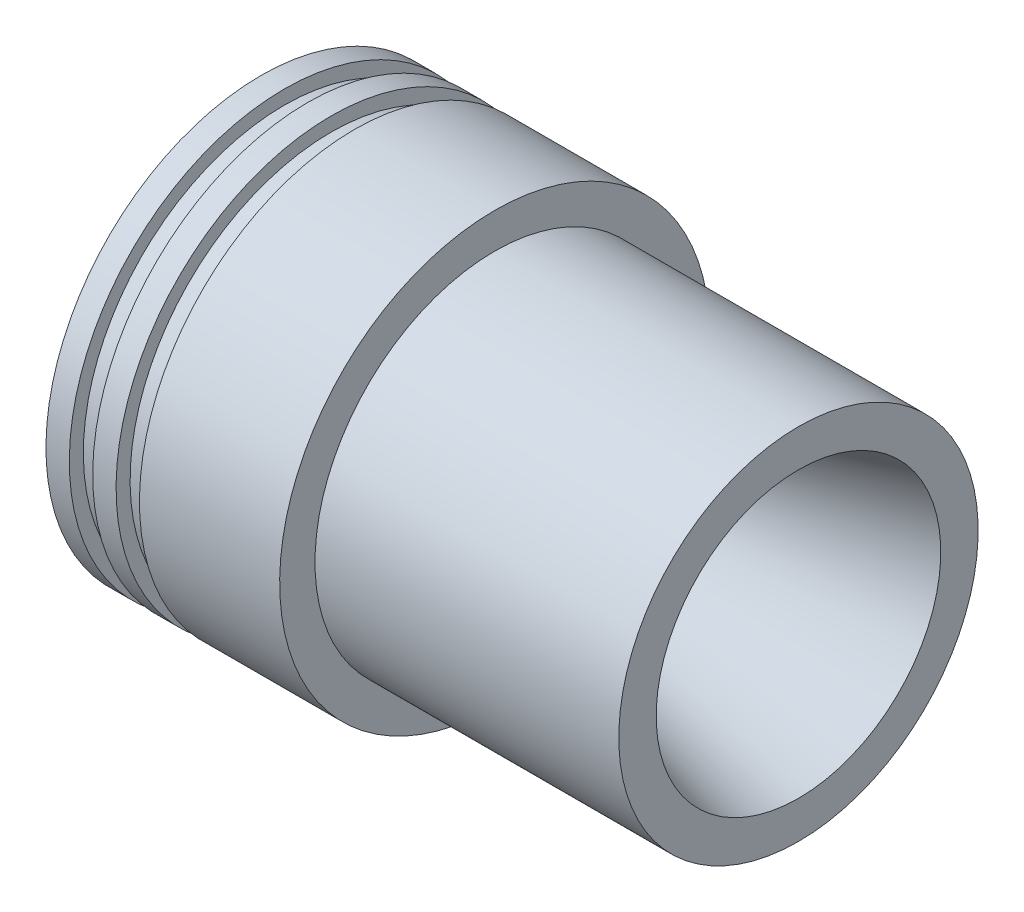
SolidWorks part; units mm, degrees
material "AISI 4130 Steel, annealed at 865C"
ref_plane "Front Plane" through (0, 0, 0) normal (0, 0, 1) x (1, 0, 0)
ref_plane "Top Plane" through (0, 0, 0) normal (0, 1, 0) x (1, 0, 0)
ref_plane "Right Plane" through (0, 0, 0) normal (1, 0, 0) x (0, 0, -1)
sketch "Sketch1" plane through (0, 0, 0) normal (0, 0, 1) x (1, 0, 0)
  line L0 (0, 0) -> (-115, 0) construction
  line L24 (-115, 36.5) -> (-71.6987, 11.5)
  line L25 (-71.6987, 11.5) -> (-70.6987, 11.5)
  line L26 (-70.6987, 11.5) -> (0, 30.4437)
  line L27 (-115, 36.5) -> (-115, 46)
  line L28 (-115, 46) -> (-110, 46)
  line L29 (-110, 46) -> (-110, 43)
  line L30 (-110, 43) -> (-105, 43)
  line L31 (-105, 43) -> (-105, 46)
  line L32 (-105, 46) -> (-100, 46)
  line L33 (-100, 46) -> (-100, 43)
  line L34 (-100, 43) -> (-95, 43)
  line L35 (-95, 43) -> (-95, 46)
  line L36 (0, 30.4437) -> (0, 38.4437)
  line L38 (-95, 46) -> (-65, 46)
  line L39 (0, 38.4437) -> (-65, 38.4437)
  line L40 (-65, 38.4437) -> (-65, 46)
  dimension "D1" = 115
  dimension "D2" = 73
  dimension "D3" = 30
  dimension "D4" = 1
  dimension "D5" = 15
  dimension "D6" = 23
  dimension "D7" = 9.5
  dimension "D8" = 5
  dimension "D9" = 3
  dimension "D10" = 5
  dimension "D11" = 5
  dimension "D12" = 5
  dimension "D13" = 50
  dimension "D14" = 8
revolve "Revolve1" add sketch "Sketch1" angle 360 about L0
